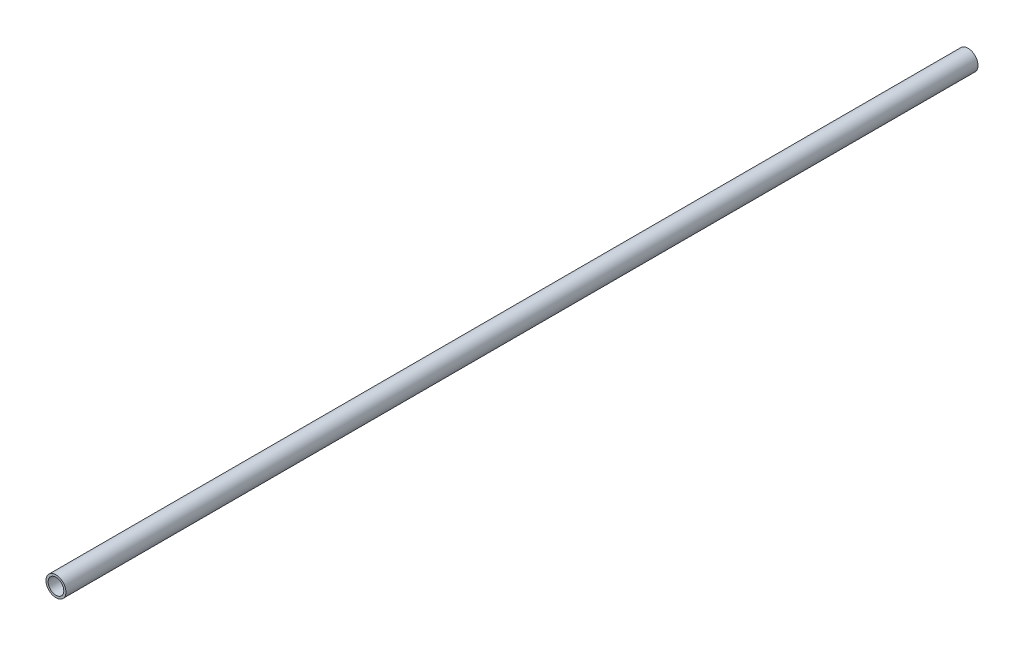
SolidWorks part; units mm, degrees
material "PVC 0.007 Plasticized"
ref_plane "Front Plane" through (0, 0, 0) normal (0, 0, 1) x (1, 0, 0)
ref_plane "Top Plane" through (0, 0, 0) normal (0, 1, 0) x (1, 0, 0)
ref_plane "Right Plane" through (0, 0, 0) normal (1, 0, 0) x (0, 0, -1)
sketch "Sketch1" plane through (0, 0, 0) normal (0, 0, 1) x (1, 0, 0)
  line L0 (10.4648, 0) -> (13.335, 0) construction
  circle A0 centre (0, 0) radius 13.335 construction
  circle A1 centre (0, 0) radius 10.4648 construction
  dimension "ID" = 20.9296
  dimension "OD" = 26.67
  dimension "Wall Thickness" = 2.8702
sketch "Sketch2" plane through (0, 0, 0) normal (1, 0, 0) x (0, 0, -1)
  line L0 (-762, 0) -> (762, 0) construction
  line L1 (-728.6625, 13.335) -> (-728.6625, -13.335) construction
  line L2 (728.6625, 13.335) -> (728.6625, -13.335) construction
  point P4 (0, 0)
  point P8 (-728.6625, 0)
  point P11 (728.6625, 0)
  dimension "Length" = 1524
  dimension "D1" = 33.3375
  dimension "D2" = 33.3375
  dimension "D3" = 26.67
sketch "Sketch3" plane through (0, 0, 0) normal (0, 0, 1) x (1, 0, 0)
  circle A0 centre (0, 0) radius 13.335
  circle A1 centre (0, 0) radius 13.335 construction
  circle A2 centre (0, 0) radius 10.4648 construction
  circle A3 centre (0, 0) radius 10.4648
extrude "Boss-Extrude1" add sketch "Sketch3" along normal up to vertex (762 mm away) and the other way up to vertex (762 mm away) up to point (0, 0, 762) other way up to point (0, 0, -762)
sketch "Sketch4" plane through (0, 0, 762) normal (0, 0, 1) x (1, 0, 0)
  circle A0 centre (0, 0) radius 10.4648 construction
  circle A1 centre (0, 0) radius 13.335
  circle A2 centre (0, 0) radius 13.335
  circle A3 centre (0, 0) radius 10.4648
  dimension "D1" = 0
extrude "Cut-Extrude2" cut sketch "Sketch4" against normal offset from surface (304.1817 mm away) 1219.8183 up to face at (10.4648, 0, -762)
equation "\"D1@Sketch2\"=\"OD@Sketch1\" * 1.25"
equation "\"D2@Sketch2\"=\"D1@Sketch2\""
equation "\"D3@Sketch2\"= \"OD@Sketch1\""
